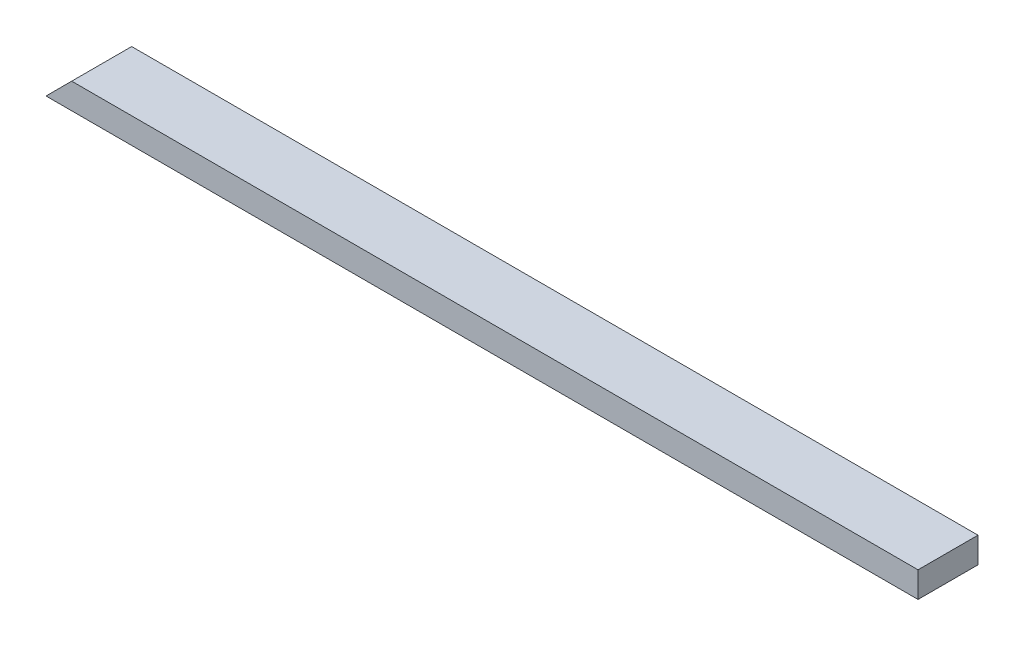
SolidWorks part; units mm, degrees
material "Pine"
ref_plane "Front Plane" through (0, 0, 0) normal (0, 0, 1) x (1, 0, 0)
ref_plane "Top Plane" through (0, 0, 0) normal (0, 1, 0) x (1, 0, 0)
ref_plane "Right Plane" through (0, 0, 0) normal (1, 0, 0) x (0, 0, -1)
sketch "Sketch1" plane through (0, 0, 0) normal (0, 1, 0) x (1, 0, 0)
  line L1 (0, 0) -> (1292.8727, 0)
  line L2 (0, 0) -> (0, 88.9)
  line L3 (0, 88.9) -> (1292.8727, 88.9)
  line L4 (1292.8727, 0) -> (1292.8727, 88.9)
  dimension "D1" = 88.9
  dimension "D2" = 1292.8727
extrude "Boss-Extrude1" add sketch "Sketch1" along normal blind 38.1
sketch "Sketch2" plane through (0, 0, 0) normal (0, 0, 1) x (1, 0, 0)
  line L0 (0, 0) -> (38.1, 38.1)
  line L1 (0, 38.1) -> (1292.8727, 38.1) construction
  line L2 (38.1, 38.1) -> (0, 38.1)
  line L3 (0, 38.1) -> (0, 0)
  dimension "D1" = 38.1
  dimension "D2" = 38.1
extrude "Cut-Extrude1" cut sketch "Sketch2" against normal through all
